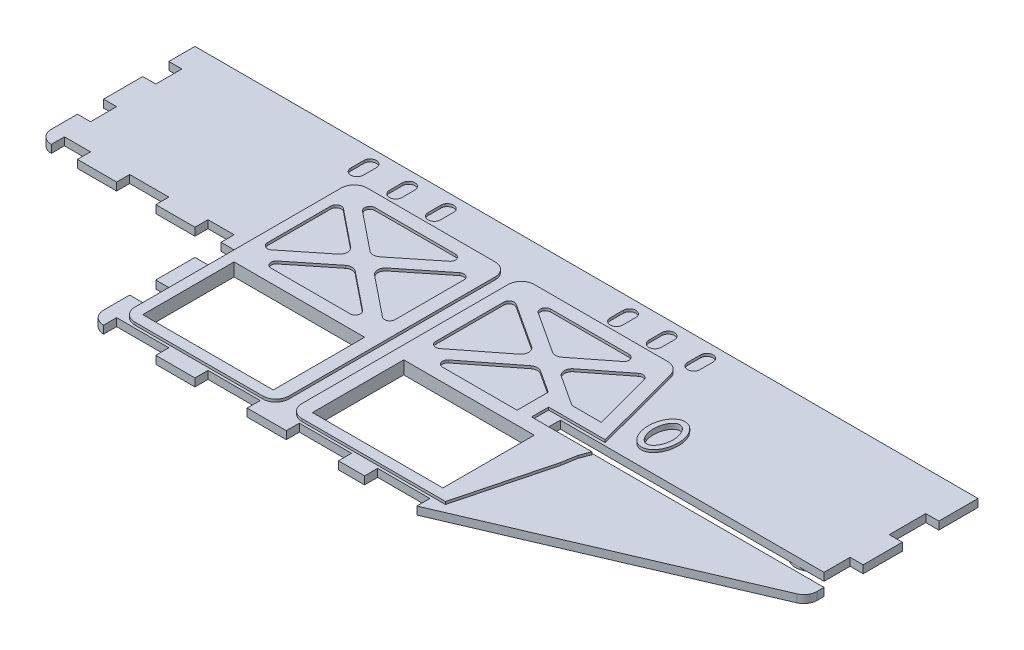
SolidWorks part; units mm, degrees
ref_plane "Front Plane" through (0, 0, 0) normal (0, 0, 1) x (1, 0, 0)
ref_plane "Top Plane" through (0, 0, 0) normal (0, 1, 0) x (1, 0, 0)
ref_plane "Right Plane" through (0, 0, 0) normal (1, 0, 0) x (0, 0, -1)
sketch "Sketch1" plane through (0, 0, 0) normal (0, 0, 1) x (1, 0, 0)
  line L0 (0, 0) -> (0, 254) construction
  line L1 (-381, 0) -> (0, 0)
  line L3 (-381, 6.35) -> (0, 6.35)
  line L4 (0, 0) -> (0, 6.35)
  line L5 (-381, 0) -> (-381, 6.35)
extrude "Boss-Extrude1" add sketch "Sketch1" along normal blind 139.7
sketch "Sketch2" plane through (0, 0, 0) normal (0, -1, 0) x (1, 0, 0)
  line L1 (-406.4, 139.7) -> (-406.4, 0) construction
  line L2 (-374.65, 76.2) -> (-292.1, 76.2)
  line L3 (-292.1, 76.2) -> (-292.1, 133.35)
  line L4 (-381, 139.7) -> (0, 139.7) construction
  line L5 (-285.75, 139.7) -> (-133.35, 139.7)
  line L6 (-133.35, 139.7) -> (-3.8486, 84.1994)
  line L7 (0, 139.7) -> (0, 0) construction
  line L8 (0, 78.3628) -> (0, 0)
  line L9 (0, 0) -> (-381, 0)
  line L10 (-381, 69.85) -> (-381, 0)
  line L11 (-381, 139.7) -> (-381, 0) construction
  arc A0 (-3.8486, 84.1994) -> (0, 78.3628) centre (-6.35, 78.3628) cw
  arc A1 (-292.1, 133.35) -> (-285.75, 139.7) centre (-285.75, 133.35) cw
  arc A3 (-381, 69.85) -> (-374.65, 76.2) centre (-374.65, 69.85) cw
  point P17 (0, 82.55)
  point P20 (-292.1, 139.7)
  point P21 (-381, 76.2)
  point P23 (-406.4, 76.2)
  dimension "D5" = 6.35
  dimension "D1" = 6.35
  dimension "D2" = 114.3
  dimension "D3" = 158.75
  dimension "D4" = 82.55
extrude "Cut-Extrude1" cut sketch "Sketch2" against normal through all
sketch "Sketch3" plane through (0, 6.35, 0) normal (0, 1, 0) x (1, 0, 0)
  line L0 (-133.35, -139.7) -> (-285.75, -139.7) construction
  line L1 (-279.4, -127) -> (-215.9, -127)
  line L2 (-279.4, -127) -> (-279.4, -82.55)
  line L3 (-279.4, -82.55) -> (-215.9, -82.55)
  line L4 (-215.9, -127) -> (-215.9, -82.55)
  line L5 (-196.85, -127) -> (-133.35, -127)
  line L6 (-196.85, -127) -> (-196.85, -82.55)
  line L7 (-196.85, -82.55) -> (-133.35, -82.55)
  line L8 (-133.35, -127) -> (-133.35, -82.55)
  line L9 (-292.1, -76.2) -> (-292.1, -133.35) construction
  dimension "D1" = 44.45
  dimension "D2" = 12.7
  dimension "D3" = 12.7
  dimension "D4" = 63.5
  dimension "D5" = 19.05
  dimension "D6" = 44.45
  dimension "D7" = 12.7
  dimension "D8" = 63.5
extrude "Cut-Extrude2" cut sketch "Sketch3" against normal through all contours L5 L8 L7 L6 | L1 L4 L3 L2
sketch "Sketch4" plane through (0, 0, 0) normal (0, -1, 0) x (1, 0, 0)
  line L0 (-285.75, 139.7) -> (-133.35, 139.7) construction
  line L1 (-278.13, 132.08) -> (-215.9, 132.08)
  line L2 (-284.48, 125.73) -> (-284.48, 25.4)
  line L3 (-278.13, 19.05) -> (-215.9, 19.05)
  line L4 (-209.55, 125.73) -> (-209.55, 25.4)
  line L5 (-127, 132.08) -> (-196.85, 132.08)
  line L7 (-131.8807, 19.05) -> (-196.85, 19.05)
  line L8 (-203.2, 125.73) -> (-203.2, 25.4)
  line L9 (-292.1, 76.2) -> (-292.1, 133.35) construction
  line L11 (-381, 0) -> (0, 0) construction
  line L12 (-215.9, 127) -> (-215.9, 82.55) construction
  line L13 (-127, 132.08) -> (-115.4772, 87.732)
  line L14 (-114.1835, 67.1935) -> (-125.7444, 23.7664)
  line L17 (-141.7163, 75.5137) -> (-141.7163, 67.1935)
  line L18 (-141.7163, 67.1935) -> (-114.1835, 67.1935)
  line L20 (-114.1835, 80.3221) -> (-115.4772, 87.732)
  line L21 (-141.7163, 75.5137) -> (-112.3314, 75.5137)
  line L22 (-112.3314, 75.5137) -> (-114.1835, 80.3221)
  arc A0 (-196.85, 132.08) -> (-203.2, 125.73) centre (-196.85, 125.73) ccw
  arc A1 (-215.9, 132.08) -> (-209.55, 125.73) centre (-215.9, 125.73) cw
  arc A2 (-278.13, 132.08) -> (-284.48, 125.73) centre (-278.13, 125.73) ccw
  arc A3 (-284.48, 25.4) -> (-278.13, 19.05) centre (-278.13, 25.4) ccw
  arc A4 (-215.9, 19.05) -> (-209.55, 25.4) centre (-215.9, 25.4) ccw
  arc A5 (-196.85, 19.05) -> (-203.2, 25.4) centre (-196.85, 25.4) cw
  arc A6 (-131.8807, 19.05) -> (-125.7444, 23.7664) centre (-131.8807, 25.4) ccw
  dimension "D3" = 6.35
  dimension "D1" = 7.62
  dimension "D2" = 7.62
  dimension "D4" = 7.62
  dimension "D5" = 19.05
  dimension "D6" = 6.35
  dimension "D7" = 6.35
  dimension "D8" = 19.05
extrude "Cut-Extrude3" cut sketch "Sketch4" against normal blind 1.27
sketch "Sketch5" plane through (0, 0, 0) normal (0, -1, 0) x (1, 0, 0)
  line L0 (-250.8616, 56.914) -> (-269.3149, 71.6766)
  line L1 (-248.4216, 50.9666) -> (-248.4331, 50.9773) construction
  line L3 (-267.7282, 76.2) -> (-229.317, 76.2)
  line L4 (-257.258, 53.8991) -> (-275.2733, 68.3113)
  line L5 (-184.3234, 76.2) -> (-146.2234, 76.2)
  line L6 (-196.85, 82.55) -> (-133.35, 82.55) construction
  line L9 (-142.8427, 29.9409) -> (-159.4602, 42.9343)
  line L10 (-227.2884, 29.9234) -> (-246.082, 44.9583)
  line L12 (-138.4514, 67.3111) -> (-158.9921, 53.9033)
  line L15 (-129.2948, 65.7051) -> (-151.5288, 51.1918)
  line L21 (-220.0267, 32.246) -> (-239.6856, 47.9731)
  line L24 (-275.269, 33.4756) -> (-257.2515, 47.954)
  line L26 (-131.8807, 25.4) -> (-122.4451, 60.8435)
  line L28 (-131.8807, 25.4) -> (-121.6899, 63.6806)
  line L30 (-121.6881, 86.3853) -> (-131.9109, 125.73)
  line L37 (-269.5564, 29.9199) -> (-250.8486, 44.9531)
  line L38 (-215.9, 34.2294) -> (-215.9, 67.7374)
  line L40 (-248.5328, 50.9091) -> (-248.3486, 51.0351) construction
  line L41 (-246.095, 56.9191) -> (-227.7259, 71.6801)
  line L42 (-248.5328, 50.9091) -> (-248.5037, 50.8894) construction
  line L43 (-228.8751, 25.4) -> (-267.9653, 25.4)
  line L44 (-248.3486, 51.0351) -> (-248.5037, 50.8894) construction
  line L45 (-279.4, 66.3279) -> (-279.4, 35.4556)
  line L46 (-239.6921, 53.9182) -> (-220.031, 69.7173)
  line L47 (-146.2234, 76.2) -> (-138.4514, 76.2)
  line L48 (-138.4514, 76.2) -> (-138.4514, 67.3111)
  line L51 (-134.0223, 31.1049) -> (-151.793, 45)
  line L52 (-121.6899, 63.6806) -> (-129.2948, 65.7051)
  line L55 (-163.4215, 54.0923) -> (-185.888, 71.6591)
  line L57 (-164.1074, 50.5642) -> (-164.3654, 50.8) construction
  line L58 (-131.9109, 125.73) -> (-196.85, 125.73)
  line L59 (-171.3529, 45.8348) -> (-192.9216, 31.7558)
  line L60 (-164.3654, 50.8) -> (-164.0586, 50.5961) construction
  line L61 (-196.85, 125.73) -> (-196.85, 25.4)
  line L62 (-164.0586, 50.5961) -> (-164.1074, 50.5642)
  line L63 (-171.0886, 52.0266) -> (-192.7454, 68.9603)
  line L65 (-163.8896, 43.1233) -> (-183.8917, 30.067)
  line L66 (-196.85, 125.73) -> (-196.85, 25.4)
  line L68 (-196.85, 25.4) -> (-131.8807, 25.4)
  line L70 (-196.85, 25.4) -> (-131.8807, 25.4)
  line L80 (-122.4451, 60.8435) -> (-148.0663, 60.8435)
  line L81 (-122.4451, 60.8435) -> (-148.0663, 60.8435)
  line L82 (-148.0663, 60.8435) -> (-148.0663, 81.8637)
  line L83 (-148.0663, 60.8435) -> (-148.0663, 81.8637)
  line L84 (-148.0663, 81.8637) -> (-120.8987, 81.8637)
  line L85 (-148.0663, 81.8637) -> (-120.8987, 81.8637)
  line L86 (-120.8987, 81.8637) -> (-121.6881, 86.3853)
  line L87 (-120.8987, 81.8637) -> (-121.6881, 86.3853)
  arc A0 (-257.258, 53.8991) -> (-257.2515, 47.954) centre (-259.6381, 50.924) cw
  arc A1 (-250.8486, 44.9531) -> (-246.082, 44.9583) centre (-248.462, 41.9831) cw
  arc A2 (-239.6856, 47.9731) -> (-239.6921, 53.9182) centre (-237.3055, 50.9483) cw
  arc A3 (-250.8616, 56.914) -> (-246.095, 56.9191) centre (-248.4815, 59.8891) ccw
  arc A4 (-267.7282, 76.2) -> (-269.3149, 71.6766) centre (-267.7282, 73.66) ccw
  arc A5 (-275.2733, 68.3113) -> (-279.4, 66.3279) centre (-276.86, 66.3279) ccw
  arc A6 (-279.4, 35.4556) -> (-275.269, 33.4756) centre (-276.86, 35.4556) ccw
  arc A7 (-267.9653, 25.4) -> (-269.5564, 29.9199) centre (-267.9653, 27.94) cw
  arc A8 (-227.2884, 29.9234) -> (-228.8751, 25.4) centre (-228.8751, 27.94) cw
  arc A9 (-220.0267, 32.246) -> (-215.9, 34.2294) centre (-218.44, 34.2294) ccw
  arc A10 (-215.9, 67.7374) -> (-220.031, 69.7173) centre (-218.44, 67.7374) ccw
  arc A11 (-227.7259, 71.6801) -> (-229.317, 76.2) centre (-229.317, 73.66) ccw
  arc A12 (-183.8917, 30.067) -> (-182.5033, 25.4) centre (-182.5033, 27.94) ccw
  arc A13 (-142.8427, 29.9409) -> (-144.4073, 25.4) centre (-144.4073, 27.94) cw
  arc A16 (-134.0223, 31.1049) -> (-130.0033, 32.4524) centre (-132.4578, 33.1058) ccw
  arc A17 (-192.9216, 31.7558) -> (-196.85, 33.8828) centre (-194.31, 33.8828) cw
  arc A18 (-196.85, 66.9593) -> (-192.7454, 68.9603) centre (-194.31, 66.9593) cw
  arc A19 (-185.888, 71.6591) -> (-184.3234, 76.2) centre (-184.3234, 73.66) cw
  arc A20 (-171.3529, 45.8348) -> (-171.0886, 52.0266) centre (-173.4355, 49.0252) ccw
  arc A21 (-163.8896, 43.1233) -> (-159.4602, 42.9343) centre (-161.807, 39.9329) cw
  arc A22 (-151.793, 45) -> (-151.5288, 51.1918) centre (-149.4462, 48.0014) cw
  arc A23 (-158.9921, 53.9033) -> (-163.4215, 54.0923) centre (-161.0746, 57.0937) cw
  point P13 (-247.9043, 50.4821)
  point P14 (-248.3486, 51.0351)
  point P39 (-243.3962, 50.9416)
  point P55 (-157.9377, 50.8)
  point P56 (-164.3654, 50.8)
  point P88 (-166.8929, 48.746)
  dimension "D5" = 3.81
  dimension "D1" = 2.54
  dimension "D4" = 2.54
  dimension "D6" = 2.54
  dimension "D7" = 2.54
  dimension "D8" = 3.81
  dimension "D3" = 6.35
  dimension "D9" = 38.1
  dimension "D2" = 6.35
extrude "Cut-Extrude4" cut sketch "Sketch5" against normal blind 1.27
sketch "Sketch6" plane through (0, 1.27, 0) normal (0, -1, 0) x (1, 0, 0)
  line L0 (-288.798, 6.985) -> (-288.798, 13.335) construction
  line L1 (-291.846, 6.985) -> (-291.846, 13.335)
  line L2 (-285.75, 6.985) -> (-285.75, 13.335)
  line L3 (-270.002, 6.985) -> (-270.002, 13.335) construction
  line L6 (-273.05, 6.985) -> (-273.05, 13.335)
  line L9 (-266.954, 6.985) -> (-266.954, 13.335)
  line L12 (-251.206, 6.985) -> (-251.206, 13.335) construction
  line L15 (-381, 0) -> (0, 0) construction
  line L17 (-254.254, 6.985) -> (-254.254, 13.335)
  line L18 (-248.158, 6.985) -> (-248.158, 13.335)
  line L19 (-162.56, 6.985) -> (-162.56, 13.335) construction
  line L20 (-165.608, 6.985) -> (-165.608, 13.335)
  line L21 (-159.512, 6.985) -> (-159.512, 13.335)
  line L22 (-143.764, 6.985) -> (-143.764, 13.335) construction
  line L23 (-146.812, 6.985) -> (-146.812, 13.335)
  line L24 (-140.716, 6.985) -> (-140.716, 13.335)
  line L25 (-124.968, 6.985) -> (-124.968, 13.335) construction
  line L26 (-128.016, 6.985) -> (-128.016, 13.335)
  line L27 (-121.92, 6.985) -> (-121.92, 13.335)
  line L28 (-381, 69.85) -> (-381, 0) construction
  arc A0 (-291.846, 6.985) -> (-285.75, 6.985) centre (-288.798, 6.985) ccw
  arc A1 (-285.75, 13.335) -> (-291.846, 13.335) centre (-288.798, 13.335) ccw
  arc A5 (-286.5205, 4.8853) -> (-286.5215, 4.9583) centre (-289.4119, 4.8853) ccw
  arc A7 (-286.5205, 4.8853) -> (-286.5215, 4.9583) centre (-289.4119, 4.8853) ccw
  arc A9 (-286.5205, 4.8853) -> (-286.5215, 4.9583) centre (-289.4119, 4.8853) ccw
  arc A10 (-273.05, 6.985) -> (-266.954, 6.985) centre (-270.002, 6.985) ccw
  arc A11 (-266.954, 13.335) -> (-273.05, 13.335) centre (-270.002, 13.335) ccw
  arc A12 (-254.254, 6.985) -> (-248.158, 6.985) centre (-251.206, 6.985) ccw
  arc A13 (-248.158, 13.335) -> (-254.254, 13.335) centre (-251.206, 13.335) ccw
  arc A14 (-165.608, 6.985) -> (-159.512, 6.985) centre (-162.56, 6.985) ccw
  arc A15 (-159.512, 13.335) -> (-165.608, 13.335) centre (-162.56, 13.335) ccw
  arc A16 (-146.812, 6.985) -> (-140.716, 6.985) centre (-143.764, 6.985) ccw
  arc A17 (-140.716, 13.335) -> (-146.812, 13.335) centre (-143.764, 13.335) ccw
  arc A18 (-128.016, 6.985) -> (-121.92, 6.985) centre (-124.968, 6.985) ccw
  arc A19 (-121.92, 13.335) -> (-128.016, 13.335) centre (-124.968, 13.335) ccw
  point P2 (-288.798, 10.16)
  point P9 (-289.4119, -1.7103)
  point P11 (-270.002, 10.16)
  point P16 (-289.4119, 0)
  point P18 (-251.206, 10.16)
  point P23 (-289.4119, 0)
  point P28 (-162.56, 10.16)
  point P30 (-289.4119, 0)
  point P41 (-143.764, 10.16)
  point P48 (-124.968, 10.16)
  point P57 (-248.158, 10.16)
  dimension "D1" = 3.048
  dimension "D2" = 6.35
  dimension "D3" = 10.16
  dimension "D4" = 95.25
  dimension "D5" = 12.7
  dimension "D6" = 12.7
  dimension "D7" = 82.55
  dimension "D8" = 12.7
  dimension "D9" = 12.7
extrude "Cut-Extrude5" cut sketch "Sketch6" against normal blind 1.27 contours L18 A13 L17 A12 | L21 A15 L20 A14 | L24 A17 L23 A16 | L27 A19 L26 A18 | L9 A11 L6 A10 | L2 A1 L1 A0
sketch "Sketch7" plane through (0, 1.27, 0) normal (0, -1, 0) x (1, 0, 0)
  line L1 (0, 0) -> (-381, 0) construction
  ellipse E0 centre (-102.3292, 50.8) end of major axis (-102.3292, 61.4382) minor radius 7.2651
  dimension "D1" = 50.8
extrude "Boss-Extrude2" add sketch "Sketch7" along normal blind 1.27
sketch "Sketch8" plane through (0, 0, 0) normal (0, -1, 0) x (1, 0, 0)
  spline S0 degree 3 poles (-102.5457, 42.7018) (-102.1128, 42.7018) (-101.9017, 42.7308) (-101.4887, 42.8387) (-101.286, 42.9186) (-100.9061, 43.1119) (-100.7263, 43.2259) (-100.3826, 43.4815) (-100.2199, 43.6228) (-99.7641, 44.0691) (-99.4978, 44.3999) (-99.0202, 45.1105) (-98.8146, 45.4829) (-98.4565, 46.2486) (-98.3038, 46.6429) (-98.0439, 47.4517) (-97.9369, 47.8667) (-97.6852, 49.111) (-97.6045, 49.9489) (-97.604, 51.2175) (-97.6245, 51.6448) (-97.7076, 52.4895) (-97.7697, 52.9068) (-98.0198, 54.1428) (-98.2685, 54.9465) (-98.8106, 56.1102) (-99.0169, 56.4835) (-99.4909, 57.1908) (-99.7614, 57.5278) (-100.2165, 57.9741) (-100.3767, 58.1135) (-100.7186, 58.3689) (-100.9015, 58.4854) (-101.2816, 58.6796) (-101.4804, 58.7586) (-101.8977, 58.8687) (-102.1082, 58.8974) (-102.5329, 58.8989) (-102.7497, 58.8705) (-103.1637, 58.7634) (-103.3649, 58.6848) (-103.748, 58.4908) (-103.9279, 58.3769) (-104.2697, 58.1234) (-104.4325, 57.9828) (-104.8923, 57.5336) (-105.1581, 57.2031) (-105.6325, 56.4987) (-105.8414, 56.1219) (-106.381, 54.9691) (-106.6338, 54.163) (-106.8884, 52.91) (-106.9508, 52.489) (-107.0335, 51.6488) (-107.0541, 51.2283) (-107.0545, 50.3866) (-107.0345, 49.9654) (-106.9523, 49.1221) (-106.8897, 48.6982) (-106.6374, 47.4509) (-106.3864, 46.6449) (-105.8458, 45.4863) (-105.6383, 45.1112) (-105.2832, 44.5821) (-105.1572, 44.4109) (-104.8873, 44.0803) (-104.7428, 43.9207) (-104.4383, 43.6226) (-104.2778, 43.4833) (-103.9365, 43.2289) (-103.7539, 43.1128) (-103.3731, 42.9188) (-103.175, 42.8404) (-102.7592, 42.7311) (-102.5457, 42.7018) (-102.1128, 42.7018) (-101.9017, 42.7308) knots -0.015625 -0.015625 0 0 0.015625 0.015625 0.03125 0.03125 0.046875 0.046875 0.0625 0.0625 0.09375 0.09375 0.125 0.125 0.15625 0.15625 0.1875 0.1875 0.25 0.25 0.28125 0.28125 0.3125 0.3125 0.375 0.375 0.40625 0.40625 0.4375 0.4375 0.453125 0.453125 0.46875 0.46875 0.484375 0.484375 0.5 0.5 0.515625 0.515625 0.53125 0.53125 0.546875 0.546875 0.5625 0.5625 0.59375 0.59375 0.625 0.625 0.6875 0.6875 0.71875 0.71875 0.75 0.75 0.78125 0.78125 0.8125 0.8125 0.875 0.875 0.90625 0.90625 0.921875 0.921875 0.9375 0.9375 0.953125 0.953125 0.96875 0.96875 0.984375 0.984375 1 1 1.015625 1.015625 1.03125 only from (-102.3292, 42.7018) to (-102.3292, 42.7018)
  spline S1 degree 3 poles (-102.5457, 42.7018) (-102.1128, 42.7018) (-101.9017, 42.7308) (-101.4887, 42.8387) (-101.286, 42.9186) (-100.9061, 43.1119) (-100.7263, 43.2259) (-100.3826, 43.4815) (-100.2199, 43.6228) (-99.7641, 44.0691) (-99.4978, 44.3999) (-99.0202, 45.1105) (-98.8146, 45.4829) (-98.4565, 46.2486) (-98.3038, 46.6429) (-98.0439, 47.4517) (-97.9369, 47.8667) (-97.6852, 49.111) (-97.6045, 49.9489) (-97.604, 51.2175) (-97.6245, 51.6448) (-97.7076, 52.4895) (-97.7697, 52.9068) (-98.0198, 54.1428) (-98.2685, 54.9465) (-98.8106, 56.1102) (-99.0169, 56.4835) (-99.4909, 57.1908) (-99.7614, 57.5278) (-100.2165, 57.9741) (-100.3767, 58.1135) (-100.7186, 58.3689) (-100.9015, 58.4854) (-101.2816, 58.6796) (-101.4804, 58.7586) (-101.8977, 58.8687) (-102.1082, 58.8974) (-102.5329, 58.8989) (-102.7497, 58.8705) (-103.1637, 58.7634) (-103.3649, 58.6848) (-103.748, 58.4908) (-103.9279, 58.3769) (-104.2697, 58.1234) (-104.4325, 57.9828) (-104.8923, 57.5336) (-105.1581, 57.2031) (-105.6325, 56.4987) (-105.8414, 56.1219) (-106.381, 54.9691) (-106.6338, 54.163) (-106.8884, 52.91) (-106.9508, 52.489) (-107.0335, 51.6488) (-107.0541, 51.2283) (-107.0545, 50.3866) (-107.0345, 49.9654) (-106.9523, 49.1221) (-106.8897, 48.6982) (-106.6374, 47.4509) (-106.3864, 46.6449) (-105.8458, 45.4863) (-105.6383, 45.1112) (-105.2832, 44.5821) (-105.1572, 44.4109) (-104.8873, 44.0803) (-104.7428, 43.9207) (-104.4383, 43.6226) (-104.2778, 43.4833) (-103.9365, 43.2289) (-103.7539, 43.1128) (-103.3731, 42.9188) (-103.175, 42.8404) (-102.7592, 42.7311) (-102.5457, 42.7018) (-102.1128, 42.7018) (-101.9017, 42.7308) knots -0.015625 -0.015625 0 0 0.015625 0.015625 0.03125 0.03125 0.046875 0.046875 0.0625 0.0625 0.09375 0.09375 0.125 0.125 0.15625 0.15625 0.1875 0.1875 0.25 0.25 0.28125 0.28125 0.3125 0.3125 0.375 0.375 0.40625 0.40625 0.4375 0.4375 0.453125 0.453125 0.46875 0.46875 0.484375 0.484375 0.5 0.5 0.515625 0.515625 0.53125 0.53125 0.546875 0.546875 0.5625 0.5625 0.59375 0.59375 0.625 0.625 0.6875 0.6875 0.71875 0.71875 0.75 0.75 0.78125 0.78125 0.8125 0.8125 0.875 0.875 0.90625 0.90625 0.921875 0.921875 0.9375 0.9375 0.953125 0.953125 0.96875 0.96875 0.984375 0.984375 1 1 1.015625 1.015625 1.03125 only from (-102.3292, 42.7018) to (-102.3292, 42.7018)
  dimension "D1" = 2.54
extrude "Cut-Extrude6" cut sketch "Sketch8" against normal blind 2.54
sketch "Sketch9" plane through (0, 1.27, 0) normal (0, -1, 0) x (1, 0, 0)
  circle A0 centre (-20.3877, 60.8315) radius 7.62
  dimension "D1" = 15.24
extrude "Boss-Extrude3" add sketch "Sketch9" along normal blind 1.27
sketch "Sketch10" plane through (0, 0, 0) normal (0, -1, 0) x (1, 0, 0)
  circle A2 centre (-20.3877, 60.8315) radius 5.08
  circle A3 centre (-20.3877, 60.8315) radius 5.08
  dimension "D1" = 2.54
extrude "Cut-Extrude7" cut sketch "Sketch10" against normal blind 2.54
sketch "Sketch14" plane through (0, 1.27, 0) normal (0, -1, 0) x (1, 0, 0)
  line L1 (-355.6, 72.8674) -> (-344.17, 72.8674)
  line L2 (-355.6, 72.8674) -> (-355.6, 66.5174)
  line L3 (-355.6, 66.5174) -> (-344.17, 66.5174)
  line L4 (-344.17, 72.8674) -> (-344.17, 66.5174)
  line L6 (-381, 69.85) -> (-381, 0) construction
  circle A0 centre (-370.84, 62.8553) radius 5.08
  dimension "D1" = 10.16
  dimension "D5" = 10.16
  dimension "D2" = 25.4
  dimension "D3" = 6.35
  dimension "D4" = 11.43
extrude "Boss-Extrude4" add sketch "Sketch14" along normal blind 1.27
ref_plane "Plane2" through (0, 3.175, 0) normal (0, -1, 0) x (-1, 0, 0)
mirror "Mirror7" about plane through (0, 3.175, 0) normal (0, -1, 0) of "Cut-Extrude3"
mirror "Mirror8" about plane through (0, 3.175, 0) normal (0, -1, 0) of "Cut-Extrude6", "Boss-Extrude2", "Cut-Extrude5", "Cut-Extrude4"
sketch "Sketch16" plane through (0, 5.08, 0) normal (0, 1, 0) x (1, 0, 0)
  line L0 (-374.65, -76.2) -> (-381, -76.2)
  line L1 (-292.1, -76.2) -> (-374.65, -76.2) construction
  line L2 (-381, -76.2) -> (-381, -57.15)
  line L3 (-381, -69.85) -> (-381, 0) construction
  line L4 (-381, -57.15) -> (-374.65, -57.15)
  line L5 (-374.65, -57.15) -> (-374.65, -44.45)
  line L6 (-374.65, -44.45) -> (-381, -44.45)
  line L7 (-381, -44.45) -> (-381, -25.4)
  line L8 (-381, -25.4) -> (-374.65, -25.4)
  line L9 (-374.65, -25.4) -> (-374.65, -12.7)
  line L11 (-374.65, -12.7) -> (-381, -12.7)
  line L12 (-381, -12.7) -> (-381, 0)
  line L13 (-381, 0) -> (-381, -76.2)
  dimension "D1" = 6.35
  dimension "D2" = 6.35
  dimension "D3" = 6.35
  dimension "D4" = 19.05
  dimension "D5" = 12.7
  dimension "D6" = 19.05
  dimension "D7" = 12.7
  dimension "D8" = 12.7
extrude "Cut-Extrude11" cut sketch "Sketch16" against normal blind 6.35 contours L11 L13 L8 L9 | L6 L13 L4 L5
sketch "Sketch17" plane through (0, 5.08, 0) normal (0, 1, 0) x (1, 0, 0)
  line L0 (-292.1, -76.2) -> (-374.65, -76.2) construction
  line L5 (-374.65, -76.2) -> (-361.95, -76.2)
  line L6 (-374.65, -76.2) -> (-374.65, -69.85)
  line L7 (-374.65, -69.85) -> (-361.95, -69.85)
  line L8 (-361.95, -76.2) -> (-361.95, -69.85)
  line L9 (-381, -69.85) -> (-381, -57.15) construction
  line L10 (-342.9, -76.2) -> (-323.85, -76.2)
  line L11 (-342.9, -76.2) -> (-342.9, -69.85)
  line L12 (-342.9, -69.85) -> (-323.85, -69.85)
  line L13 (-323.85, -76.2) -> (-323.85, -69.85)
  line L14 (-304.8, -76.2) -> (-292.1, -76.2)
  line L15 (-304.8, -76.2) -> (-304.8, -69.85)
  line L16 (-304.8, -69.85) -> (-292.1, -69.85)
  line L17 (-292.1, -76.2) -> (-292.1, -69.85)
  line L18 (-292.1, -133.35) -> (-292.1, -76.2) construction
  line L19 (-292.1, -120.65) -> (-285.75, -120.65)
  line L20 (-292.1, -120.65) -> (-292.1, -107.95)
  line L21 (-292.1, -107.95) -> (-285.75, -107.95)
  line L24 (-133.35, -139.7) -> (-285.75, -139.7) construction
  line L25 (-292.1, -88.9) -> (-285.75, -88.9)
  line L26 (-292.1, -88.9) -> (-292.1, -76.2)
  line L27 (-292.1, -76.2) -> (-285.75, -76.2)
  line L29 (-285.75, -139.7) -> (-260.35, -139.7)
  line L30 (-285.75, -139.7) -> (-285.75, -133.35)
  line L32 (-260.35, -139.7) -> (-260.35, -133.35)
  line L35 (-241.3, -139.7) -> (-215.9, -139.7)
  line L36 (-241.3, -139.7) -> (-241.3, -133.35)
  line L38 (-215.9, -139.7) -> (-215.9, -133.35)
  line L39 (-196.85, -139.707) -> (-171.45, -139.707)
  line L40 (-196.85, -139.707) -> (-196.85, -133.35)
  line L42 (-171.45, -139.707) -> (-171.45, -133.35)
  line L43 (-133.35, -133.35) -> (-158.75, -133.35)
  line L44 (-158.75, -139.7) -> (-133.35, -139.7)
  line L45 (-158.75, -139.7) -> (-158.75, -133.35)
  line L47 (-133.35, -139.7) -> (-133.35, -133.35)
  line L48 (-171.45, -133.35) -> (-196.85, -133.35)
  line L49 (-215.9, -133.35) -> (-241.3, -133.35)
  line L50 (-260.35, -133.35) -> (-285.75, -133.35)
  line L51 (-285.75, -120.65) -> (-285.75, -107.95)
  line L52 (-285.75, -88.9) -> (-285.75, -76.2)
  point P16 (-361.95, -73.025)
  dimension "D1" = 6.35
  dimension "D2" = 6.35
  dimension "D3" = 6.35
  dimension "D4" = 6.35
  dimension "D5" = 12.7
  dimension "D6" = 19.05
  dimension "D7" = 19.05
  dimension "D8" = 19.05
  dimension "D9" = 12.7
  dimension "D10" = 12.7
  dimension "D11" = 19.05
  dimension "D12" = 12.7
  dimension "D13" = 0
  dimension "D14" = 6.35
  dimension "D15" = 6.35
  dimension "D16" = 25.4
  dimension "D17" = 19.05
  dimension "D18" = 25.4
  dimension "D19" = 19.05
  dimension "D20" = 25.4
  dimension "D21" = 25.4
  dimension ".50" = 12.7
  dimension "D22" = 6.35
extrude "Cut-Extrude12" cut sketch "Sketch17" against normal blind 6.35
sketch "Sketch18" plane through (0, 5.08, 0) normal (0, 1, 0) x (1, 0, 0)
  line L0 (0, 0) -> (0, -78.3628) construction
  line L1 (0, -19.05) -> (-6.35, -19.05)
  line L2 (0, -19.05) -> (0, -36.83)
  line L3 (0, -36.83) -> (-6.35, -36.83)
  line L4 (-6.35, -19.05) -> (-6.35, -36.83)
  line L5 (-381, 0) -> (0, 0) construction
  line L6 (0, -55.88) -> (-6.35, -55.88)
  line L7 (0, -55.88) -> (0, -74.93)
  line L8 (0, -74.93) -> (-6.35, -74.93)
  line L9 (-6.35, -55.88) -> (-6.35, -74.93)
  dimension "D1" = 6.35
  dimension "D2" = 6.35
  dimension "D3" = 19.05
  dimension "D4" = 17.78
  dimension "D5" = 19.05
  dimension "D6" = 19.05
extrude "Cut-Extrude13" cut sketch "Sketch18" against normal blind 6.35
sketch "Sketch19" plane through (0, 0, 0) normal (0, -1, 0) x (1, 0, 0)
  line L1 (-6.35, 74.93) -> (-134.62, 74.93)
  line L2 (-6.35, 74.93) -> (-6.35, 68.58)
  line L3 (-6.35, 68.58) -> (-134.62, 68.58)
  line L4 (-134.62, 74.93) -> (-134.62, 68.58)
  dimension "D1" = 6.35
  dimension "D2" = 128.27
extrude "Cut-Extrude14" cut sketch "Sketch19" against normal blind 6.35
